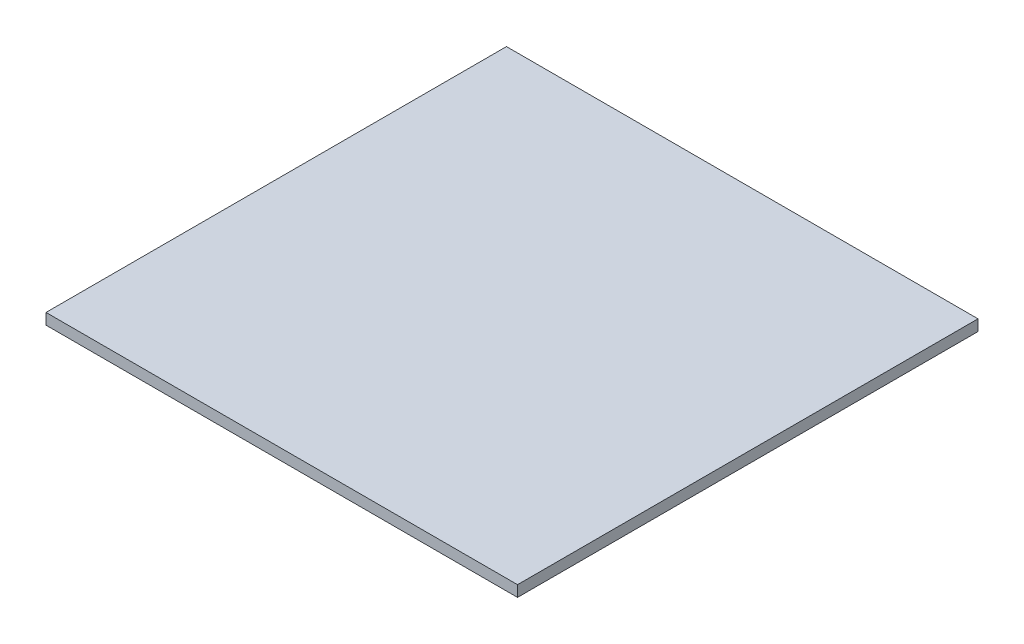
SolidWorks part; units mm, degrees
material "ASTM A36 Steel"
ref_plane "Front Plane" through (0, 0, 0) normal (0, 0, 1) x (1, 0, 0)
ref_plane "Top Plane" through (0, 0, 0) normal (0, 1, 0) x (1, 0, 0)
ref_plane "Right Plane" through (0, 0, 0) normal (1, 0, 0) x (0, 0, -1)
sketch "Sketch1" plane through (0, 0, 0) normal (0, 1, 0) x (1, 0, 0)
  line L1 (101.6, 99.2188) -> (-101.6, 99.2188)
  line L2 (101.6, 99.2188) -> (101.6, -99.2187)
  line L3 (101.6, -99.2187) -> (-101.6, -99.2188)
  line L4 (-101.6, 99.2188) -> (-101.6, -99.2188)
  line L5 (101.6, 99.2188) -> (-101.6, -99.2188) construction
  line L6 (101.6, -99.2187) -> (-101.6, 99.2188) construction
  point P0 (0, 0)
  dimension "D1" = 198.4375
  dimension "D2" = 203.2
extrude "Boss-Extrude1" add sketch "Sketch1" along normal blind 4.7625
